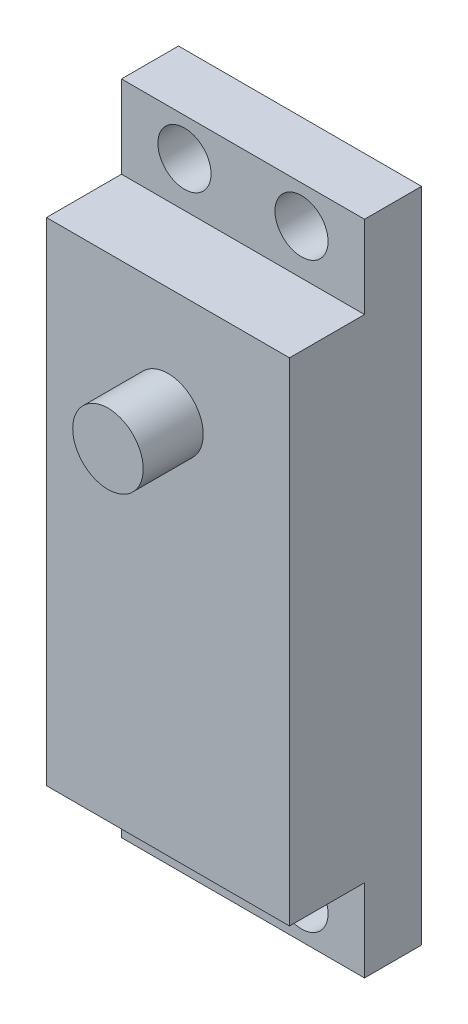
SolidWorks part; units mm, degrees
ref_plane "Front Plane" through (0, 0, 0) normal (0, 0, 1) x (1, 0, 0)
ref_plane "Top Plane" through (0, 0, 0) normal (0, 1, 0) x (1, 0, 0)
ref_plane "Right Plane" through (0, 0, 0) normal (1, 0, 0) x (0, 0, -1)
sketch "Sketch1" plane through (0, 0, 0) normal (0, 0, 1) x (1, 0, 0)
  line L0 (10.287, -27.813) -> (-10.287, 27.813) construction
  line L1 (-10.287, -27.813) -> (10.287, -27.813)
  line L2 (-10.287, -27.813) -> (-10.287, 27.813)
  line L3 (-10.287, 27.813) -> (10.287, 27.813)
  line L4 (10.287, -27.813) -> (10.287, 27.813)
  line L5 (10.287, 27.813) -> (-10.287, -27.813) construction
  point P4 (0, 0)
  dimension "D1" = 55.626
  dimension "D2" = 20.574
extrude "Boss-Extrude1" add sketch "Sketch1" along normal blind 11.176
sketch "Sketch2" plane through (0, 0, 11.176) normal (0, 0, 1) x (1, 0, 0)
  line L0 (0, 27.813) -> (0, -27.813) construction
  line L1 (10.287, 27.813) -> (-10.287, 27.813) construction
  line L2 (-10.287, -27.813) -> (10.287, -27.813) construction
  circle A0 centre (0, 11.557) radius 2.9845
  dimension "D1" = 5.969
  dimension "D2" = 16.256
extrude "Boss-Extrude2" add sketch "Sketch2" along normal blind 5.08
sketch "Sketch3" plane through (0, 0, 0) normal (0, 0, -1) x (-1, 0, 0)
  line L0 (4.953, 24.638) -> (10.287, 24.638) construction
  line L2 (10.287, 27.813) -> (10.287, -27.813) construction
  line L5 (-10.287, 27.813) -> (10.287, 27.813) construction
  dimension "D1" = 3.175
  dimension "D2" = 5.334
hole_wizard "#8 Clearance Hole1" positions "Sketch5" profile "Sketch4" hole size "#8" standard "ANSI Inch" end condition through all
sketch "Sketch5" plane through (0, 0, 0) normal (0, 0, -1) x (-1, 0, 0)
  point P0 (4.953, 24.638)
sketch "Sketch4" plane through (-4.953, 24.638, 0) normal (1, 0, 0) x (0, 1, 0)
  line L0 (0, 0) -> (0, 16.256)
  line L1 (0, 16.256) -> (2.2479, 16.256)
  line L2 (2.2479, 16.256) -> (2.2479, 0)
  line L5 (2.2479, 0) -> (0, 0)
  line L11 (0, -6.35) -> (0, 107.95) construction
  dimension "Thru Hole Dia." = 4.4958
  dimension "Thru Hole Depth" = 16.256
mirror "Mirror1" about plane through (0, 0, 0) normal (1, 0, 0) of "#8 Clearance Hole1"
mirror "Mirror2" about plane through (0, 0, 0) normal (0, 1, 0) of "Mirror1", "#8 Clearance Hole1"
sketch "Sketch6" plane through (-10.287, 0, 0) normal (-1, 0, 0) x (0, 0, 1)
  line L1 (11.176, -27.813) -> (4.826, -27.813)
  line L2 (11.176, -27.813) -> (11.176, -20.828)
  line L3 (11.176, -20.828) -> (4.826, -20.828)
  line L4 (4.826, -27.813) -> (4.826, -20.828)
  line L5 (11.176, 27.813) -> (4.826, 27.813)
  line L6 (11.176, 27.813) -> (11.176, 20.828)
  line L7 (11.176, 20.828) -> (4.826, 20.828)
  line L8 (4.826, 27.813) -> (4.826, 20.828)
  dimension "D1" = 6.35
  dimension "D2" = 6.35
  dimension "D3" = 6.985
  dimension "D4" = 6.985
extrude "Cut-Extrude1" cut sketch "Sketch6" against normal through all
